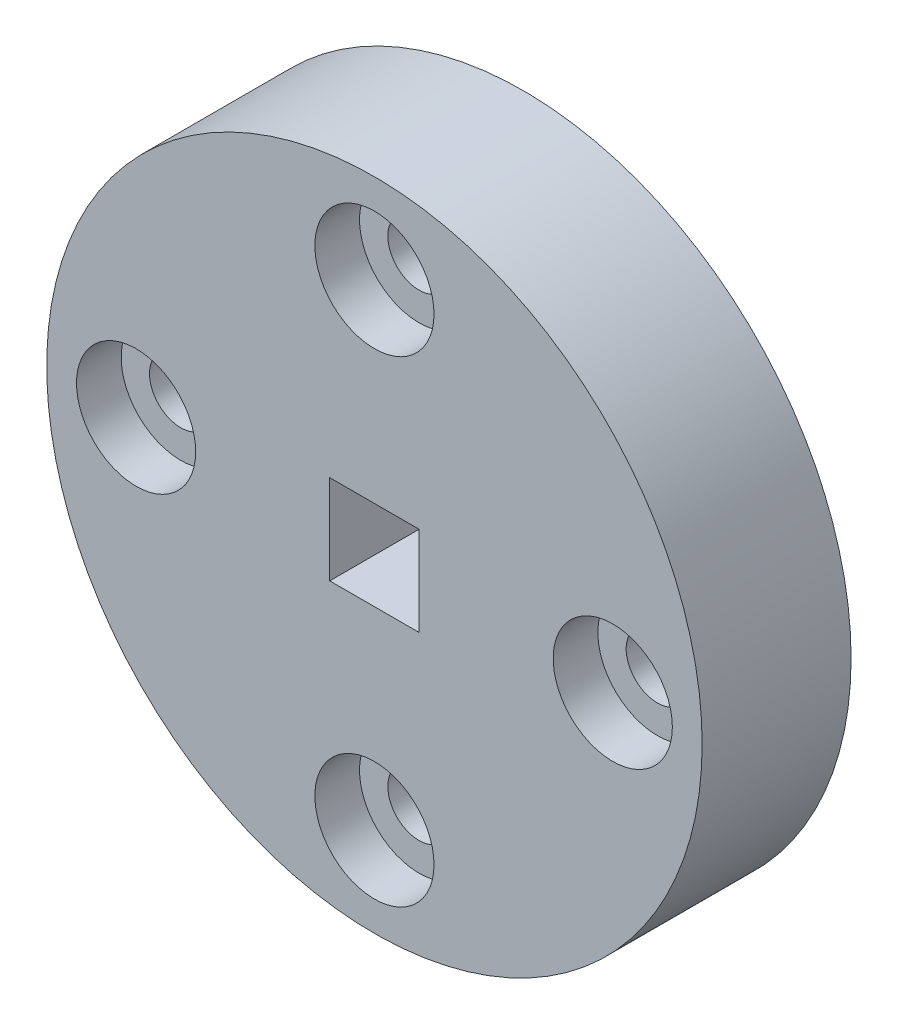
SolidWorks part; units mm, degrees
ref_plane "Front Plane" through (0, 0, 0) normal (0, 0, 1) x (1, 0, 0)
ref_plane "Top Plane" through (0, 0, 0) normal (0, 1, 0) x (1, 0, 0)
ref_plane "Right Plane" through (0, 0, 0) normal (1, 0, 0) x (0, 0, -1)
sketch "Sketch1" plane through (0, 0, 0) normal (0, 0, 1) x (1, 0, 0)
  arc A0 (0, -9.05) -> (0, -6.95) centre (0, -8) ccw
  arc A1 (-10.9972, 0.2472) -> (10.9397, -1.15) centre (0, 0) ccw
  arc A2 (10.9397, -1.15) -> (11, 0) centre (0, 0) ccw
  arc A3 (11, 0) -> (10.9671, 0.85) centre (0, 0) ccw
  arc A4 (10.9671, 0.85) -> (-10.9972, 0.2472) centre (0, 0) ccw
  arc A5 (0, -6.95) -> (0, -9.05) centre (0, -8) ccw
  arc A6 (8, 1.05) -> (8, -1.05) centre (8, 0) ccw
  arc A7 (8, -1.05) -> (8, 1.05) centre (8, 0) ccw
  arc A8 (0, 9.05) -> (0, 6.95) centre (0, 8) ccw
  arc A9 (0, 6.95) -> (0, 9.05) centre (0, 8) ccw
  arc A10 (-9.05, -0.0001) -> (-8, -1.05) centre (-8, 0) ccw
  arc A11 (-8, 1.05) -> (-9.05, -0.0001) centre (-8, 0) ccw
  arc A12 (-8, -1.05) -> (-8, 1.05) centre (-8, 0) ccw
extrude "Boss-Extrude1" add sketch "Sketch1" along normal blind 5
sketch "Sketch2" plane through (0, 0, 5) normal (0, 0, 1) x (1, 0, 0)
  line L1 (-1.5, -1.5) -> (1.5, -1.5)
  line L2 (-1.5, -1.5) -> (-1.5, 1.5)
  line L3 (-1.5, 1.5) -> (1.5, 1.5)
  line L4 (1.5, -1.5) -> (1.5, 1.5)
  line L5 (-1.5, -1.5) -> (1.5, 1.5) construction
  line L6 (-1.5, 1.5) -> (1.5, -1.5) construction
  point P0 (0, 0)
  dimension "D1" = 3
  dimension "D2" = 3
sketch "Sketch5" plane through (0, 0, 5) normal (0, 0, 1) x (1, 0, 0)
  circle A0 centre (8, 0) radius 2
  circle A1 centre (0, -8) radius 2
  circle A2 centre (-8, 0) radius 2
  circle A3 centre (0, 8) radius 2
extrude "Cut-Extrude1" cut sketch "Sketch5" against normal blind 1.5
extrude "Cut-Extrude2" cut sketch "Sketch2" against normal blind 10 contours L1 L4 L3 L2
